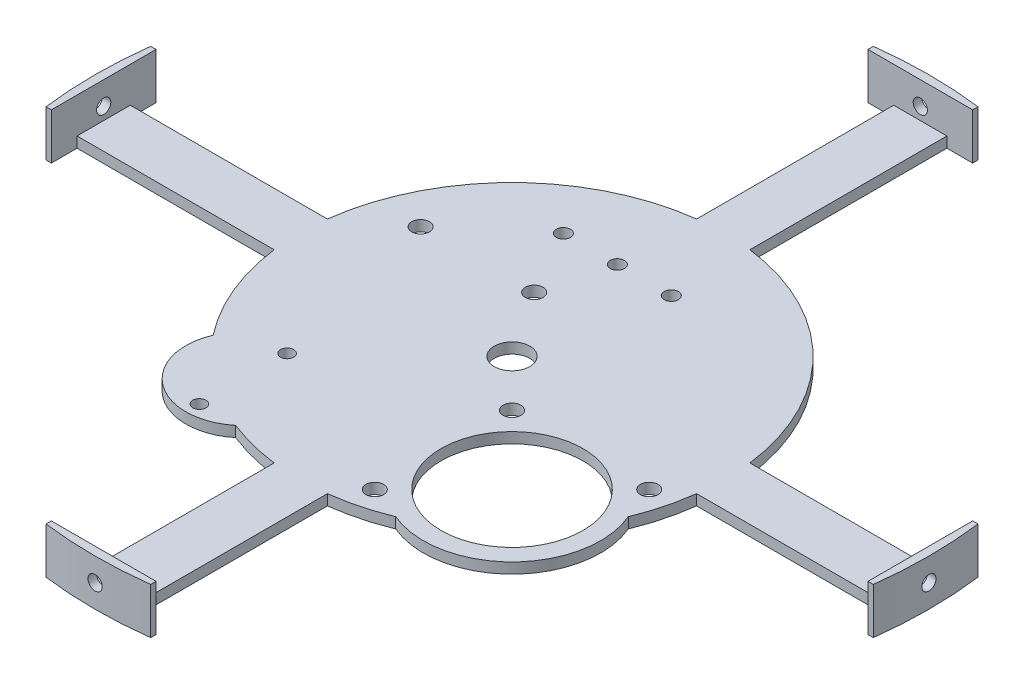
SolidWorks part; units mm, degrees
material "6061-T6 (SS)"
ref_plane "Front Plane" through (0, 0, 0) normal (0, 0, 1) x (1, 0, 0)
ref_plane "Top Plane" through (0, 0, 0) normal (0, 1, 0) x (1, 0, 0)
ref_plane "Right Plane" through (0, 0, 0) normal (1, 0, 0) x (0, 0, -1)
sketch "Sketch1" plane through (0, 0, 0) normal (0, 1, 0) x (1, 0, 0)
  circle A0 centre (0, 0) radius 76.2
  dimension "D1" = 152.4
extrude "Boss-Extrude1" add sketch "Sketch1" along normal blind 3.81 contours A0
sketch "Sketch3" plane through (0, 0, 0) normal (0, -1, 0) x (-1, 0, 0)
  line L0 (9.525, -9.525) -> (148.9207, -9.525)
  line L3 (9.525, 9.525) -> (148.9207, 9.525)
  line L6 (-9.525, -9.525) -> (-9.525, -148.9207)
  line L7 (9.525, -9.525) -> (9.525, -148.9207)
  line L9 (-9.525, 9.525) -> (-148.9207, 9.525)
  line L10 (-9.525, -9.525) -> (-148.9207, -9.525)
  line L12 (9.525, 9.525) -> (9.525, 148.9207)
  line L13 (-9.525, 9.525) -> (-9.525, 148.9207)
  line L14 (0, 0) -> (149.225, 0) construction
  line L15 (13.694, 9.525) -> (13.694, -9.525) construction
  line L16 (0, 149.225) -> (0, -149.225) construction
  arc A0 (148.9207, -9.525) -> (148.9207, 9.525) centre (0, 0) ccw
  arc A1 (-9.525, -148.9207) -> (9.525, -148.9207) centre (0, 0) ccw
  arc A2 (-148.9207, 9.525) -> (-148.9207, -9.525) centre (0, 0) ccw
  arc A3 (9.525, 148.9207) -> (-9.525, 148.9207) centre (0, 0) ccw
  circle A4 centre (0, 0) radius 76.2 construction
  point P22 (0, 0)
  dimension "D2" = 19.05
  dimension "D3" = 298.45
  dimension "D4" = 13.694
  dimension "D1" = 4
extrude "Boss-Extrude3" add sketch "Sketch3" against normal blind 3.81
sketch "Sketch5" plane through (0, 3.81, 0) normal (0, 1, 0) x (1, 0, 0)
  circle A1 centre (0, 0) radius 6.35
  dimension "D1" = 12.7
extrude "Cut-Extrude1" cut sketch "Sketch5" against normal through all
sketch "Sketch7" plane through (0, 3.81, 0) normal (0, 1, 0) x (1, 0, 0)
  line L0 (0, 149.225) -> (0, 0) construction
  line L2 (18.7397, 148.0437) -> (18.7397, 146.1387)
  line L3 (18.7397, 146.1387) -> (-18.7397, 146.1387)
  line L4 (-18.7397, 148.0437) -> (-18.7397, 146.1387)
  line L5 (9.525, 148.9207) -> (9.525, 75.6023) construction
  line L6 (-148.9207, 9.525) -> (-75.6023, 9.525) construction
  arc A0 (18.7397, 148.0437) -> (-18.7397, 148.0437) centre (0, 0) ccw
  dimension "D1" = 149.225
  dimension "D2" = 9.2147
  dimension "D3" = 136.6137
extrude "Boss-Extrude4" add sketch "Sketch7" along normal blind 12.7 and the other way blind 3.81
sketch "Sketch9" plane through (0, 0, 0) normal (0, -1, 0) x (1, 0, 0)
  circle A0 centre (-56.515, -23.8125) radius 3.175
  circle A1 centre (-15.875, -23.8125) radius 3.175
  dimension "D1" = 6.35
extrude "Cut-Extrude4" cut sketch "Sketch9" against normal up to surface (3.81 mm away) up to face at (0, 3.81, 0.3668)
sketch "Sketch11" plane through (0, 3.81, 0) normal (0, 1, 0) x (1, 0, 0)
  circle A0 centre (41.275, -41.275) radius 25.4
  circle A1 centre (41.275, -41.275) radius 31.75
  dimension "D1" = 50.8
  dimension "D2" = 63.5
extrude "Boss-Extrude5" add sketch "Sketch11" against normal blind 3.81
sketch "Sketch12" plane through (0, 3.81, 0) normal (0, 1, 0) x (1, 0, 0)
  circle A0 centre (41.275, -41.275) radius 25.4
  dimension "D1" = 50.8
extrude "Cut-Extrude5" cut sketch "Sketch12" against normal blind 3.81
sketch "Sketch13" plane through (0, 3.81, 0) normal (0, 1, 0) x (1, 0, 0)
  circle A0 centre (-41.1687, -55.0334) radius 20.5295
  circle A1 centre (-41.1711, -70.7309) radius 2.3622
  circle A2 centre (-41.1663, -39.3359) radius 2.3622
  dimension "D1" = 4.7244
  dimension "D2" = 41.0591
extrude "Boss-Extrude7" add sketch "Sketch13" against normal blind 3.81
sketch "Sketch14" plane through (0, 3.81, 0) normal (0, 1, 0) x (1, 0, 0)
  circle A0 centre (-41.1663, -39.3359) radius 2.3622
  dimension "D1" = 4.7244
extrude "Cut-Extrude6" cut sketch "Sketch14" against normal blind 3.81
sketch "Sketch15" plane through (0, 3.81, 0) normal (0, 1, 0) x (1, 0, 0)
  circle A0 centre (16.7207, -16.7207) radius 3.175
  circle A1 centre (65.8293, -16.7207) radius 3.175
  circle A2 centre (16.7207, -65.8293) radius 3.175
  dimension "D1" = 6.35
extrude "Cut-Extrude7" cut sketch "Sketch15" against normal blind 3.81
ref_plane "Plane2" through (0, 0, -149.225) normal (0, 0, -1) x (-1, 0, 0)
sketch "Sketch18" plane through (0, 0, -149.225) normal (0, 0, -1) x (-1, 0, 0)
  line L0 (0, 16.51) -> (0, 0) construction
  line L1 (18.7397, 16.51) -> (-18.7397, 16.51) construction
  circle A0 centre (0, 8.255) radius 2.54
  dimension "D1" = 5.08
hole_wizard "Tap Drill for 1/4-20 Tap1" positions "Sketch19" profile "Sketch20" hole size "1/4-20" standard "ANSI Inch" end condition up to next
sketch "Sketch19" plane through (0, 0, -149.225) normal (0, 0, -1) x (-1, 0, 0)
  point P0 (0, 8.255)
sketch "Sketch20" plane through (0, 8.255, -149.225) normal (1, 0, 0) x (0, 1, 0)
  line L0 (0, 0) -> (0, 3.0873)
  line L1 (0, 3.0873) -> (2.5527, 3.0873)
  line L2 (2.5527, 3.0873) -> (2.5527, 0)
  line L5 (2.5527, 0) -> (0, 0)
  line L11 (0, -6.35) -> (0, 107.95) construction
  dimension "Thru Hole Dia." = 5.1054
  dimension "Thru Hole Depth" = 3.0873
pattern_circular "CirPattern1" count 4 over 360 about axis through (0, 0, 0) along (0, 1, 0) of "Tap Drill for 1/4-20 Tap1", "Boss-Extrude4"
sketch "Sketch22" plane through (0, 3.81, 0) normal (0, 1, 0) x (1, 0, 0)
  circle A7 centre (9.6762, 47.3273) radius 2.54
  circle A8 centre (-9.6293, 47.3273) radius 2.54
  circle A9 centre (-28.9348, 47.3273) radius 2.54
extrude "Cut-Extrude8" cut sketch "Sketch22" against normal blind 17.78
equation "\"BoltClearance\"= .1285"
equation "\"Actuator_Plate\"=6"
equation "\"Rocket Diameter\"= 12"
equation "\"D3@Sketch3\"=\"Rocket Diameter\"-.25"
equation "\"D1@Sketch7\"=\"Rocket Diameter\"/2-.125"
